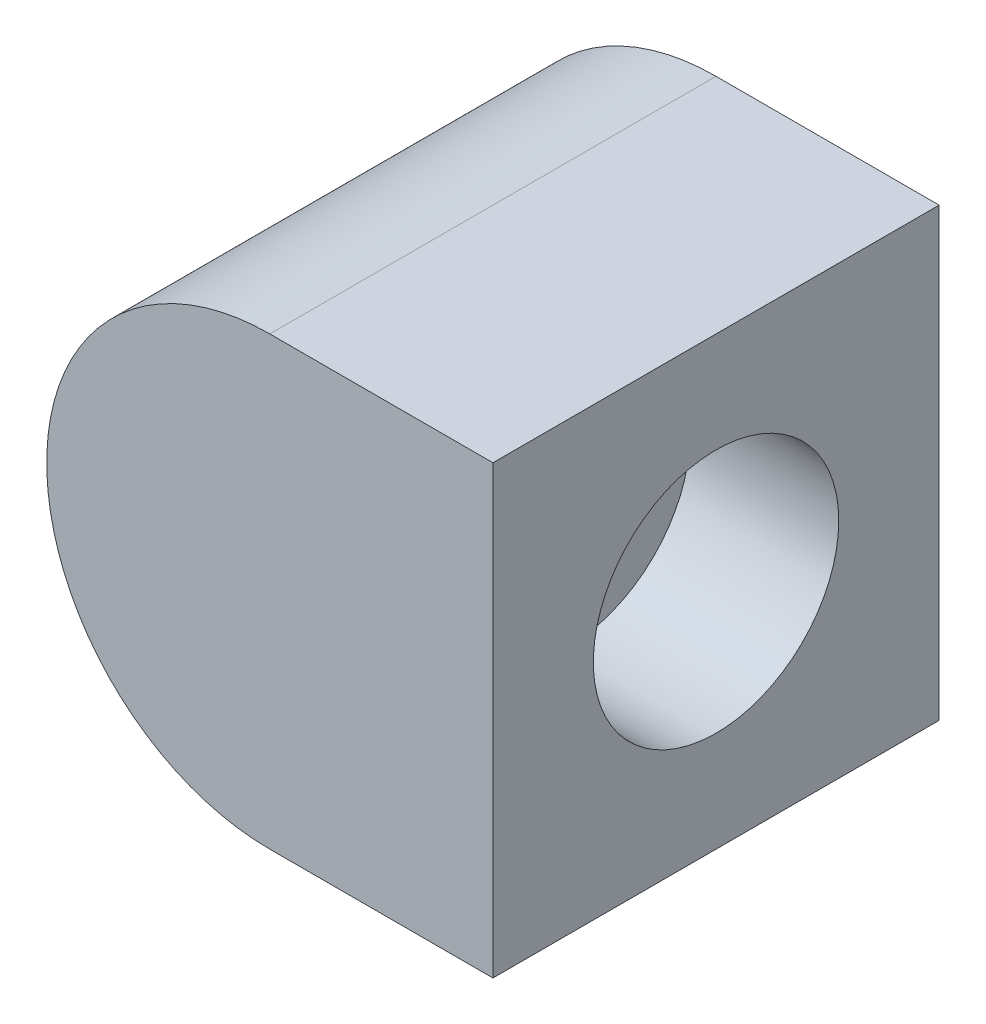
SolidWorks part; units mm, degrees
ref_plane "Plano frontal" through (0, 0, 0) normal (0, 0, 1) x (1, 0, 0)
ref_plane "Plano superior" through (0, 0, 0) normal (0, 1, 0) x (1, 0, 0)
ref_plane "Plano direito" through (0, 0, 0) normal (1, 0, 0) x (0, 0, -1)
sketch "Esboço1" plane through (0, 0, 0) normal (0, 0, 1) x (1, 0, 0)
  line L0 (0, 3) -> (3, 3)
  line L1 (3, 3) -> (3, -3)
  line L2 (3, -3) -> (0, -3)
  arc A0 (0, 3) -> (0, -3) centre (0, 0) ccw
  dimension "D1" = 3
  dimension "D2" = 3
extrude "Ressalto-extrusão1" add sketch "Esboço1" along normal blind 6
sketch "Esboço3" plane through (3, 0, 0) normal (1, 0, 0) x (0, 0, -1)
  line L0 (-6, 3) -> (0, 3) construction
  line L1 (-3, 3) -> (-3, 0) construction
  line L2 (-3, 0) -> (0, 0) construction
  circle A0 centre (-3, 0) radius 1.65
  dimension "D1" = 3.3
extrude "Corte-extrusão1" cut sketch "Esboço3" against normal blind 2
